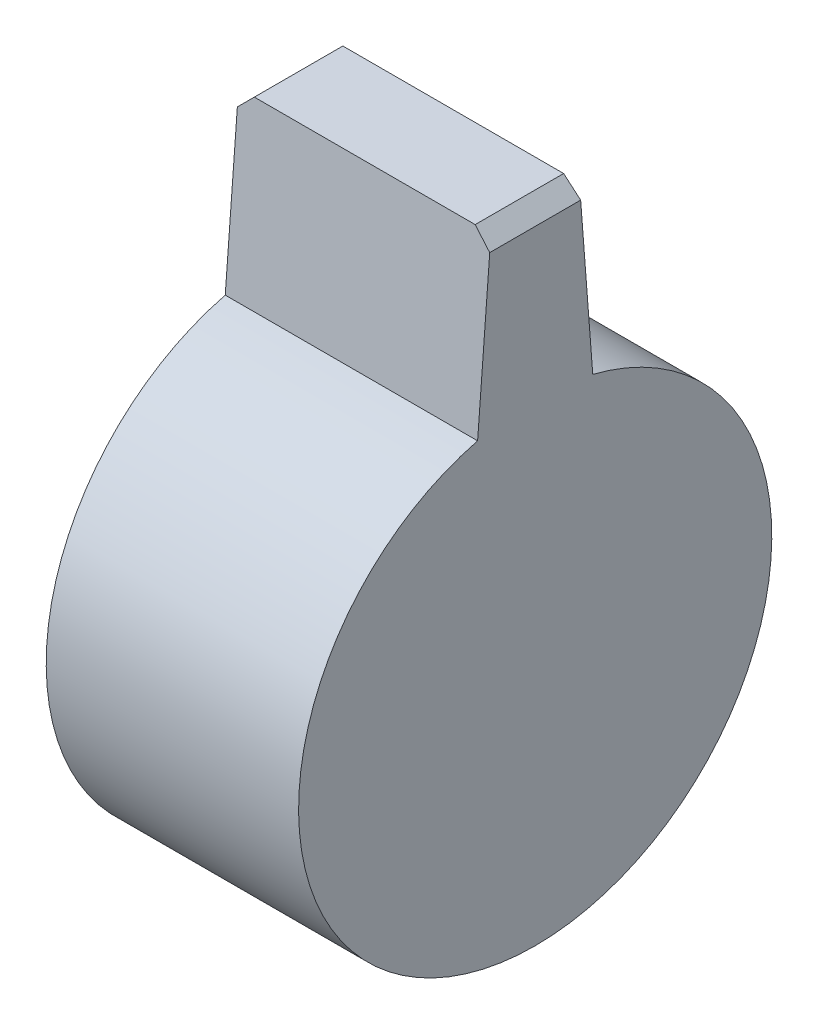
SolidWorks part; units mm, degrees
material "ABS"
ref_plane "Front Plane" through (0, 0, 0) normal (0, 0, 1) x (1, 0, 0)
ref_plane "Top Plane" through (0, 0, 0) normal (0, 1, 0) x (1, 0, 0)
ref_plane "Right Plane" through (0, 0, 0) normal (1, 0, 0) x (0, 0, -1)
sketch "Sketch1" plane through (0, 0, 0) normal (1, 0, 0) x (0, 0, -1)
  line L0 (-3.65, 14.5491) -> (-2.805, 25.5)
  line L1 (-2.805, 25.5) -> (2.805, 25.5)
  line L2 (2.805, 25.5) -> (3.65, 14.5491)
  line L3 (0, 25.5) -> (0, 0) construction
  line L4 (-3.65, 14.5491) -> (3.65, 14.5491) construction
  arc A0 (-3.65, 14.5491) -> (3.65, 14.5491) centre (0, 0) ccw
  dimension "D1" = 30
  dimension "D2" = 25.5
  dimension "D3" = 5.61
  dimension "D4" = 7.3
extrude "Boss-Extrude1" add sketch "Sketch1" along normal blind 16 contours A0 L2 L1 L0
chamfer "Chamfer1" distance 1 angle 45 2 edges at (16, 25.5, 0) (0, 25.5, 0)
equation "\"D2@Sketch1\"=\"D1@Sketch1\"/2+19-8.5"
